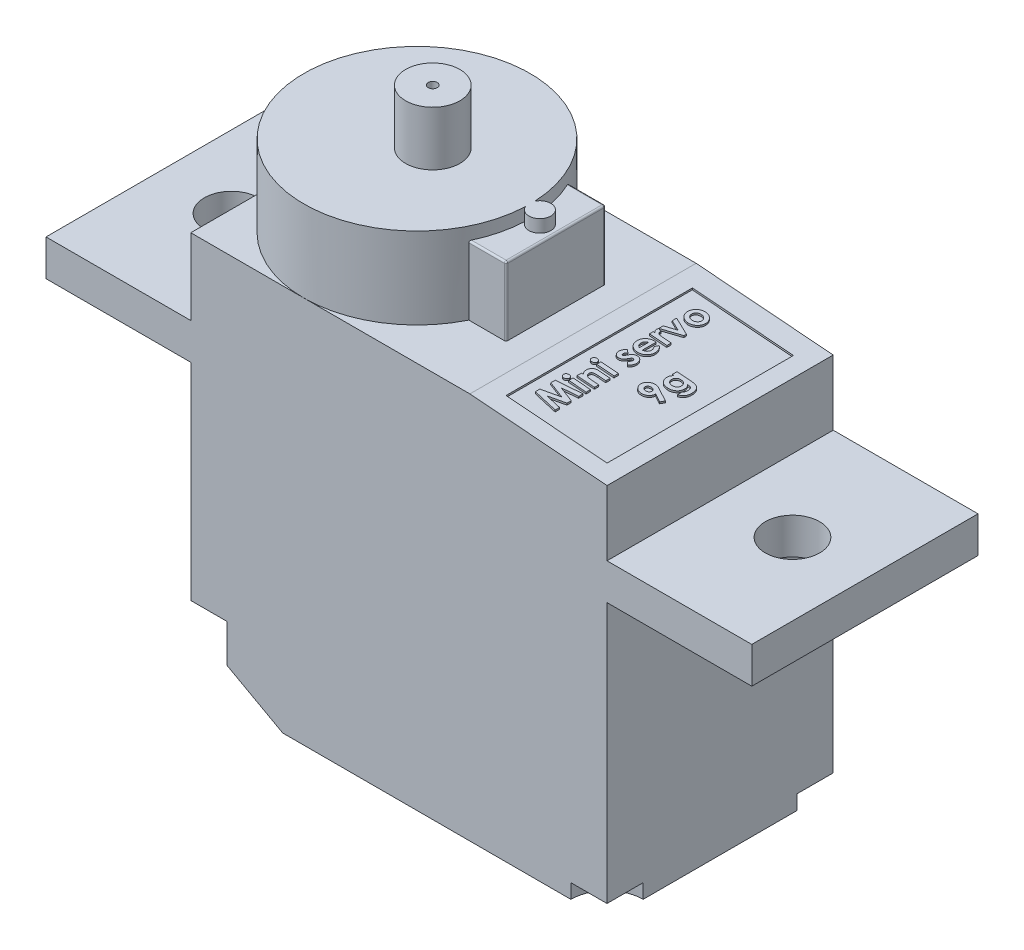
SolidWorks part; units mm, degrees
other "Camera1"
material "ABS"
ref_plane "Front Plane" through (0, 0, 0) normal (0, 0, 1) x (1, 0, 0)
ref_plane "Top Plane" through (0, 0, 0) normal (0, 1, 0) x (1, 0, 0)
ref_plane "Right Plane" through (0, 0, 0) normal (1, 0, 0) x (0, 0, -1)
sketch "Sketch1" plane through (0, 0, 0) normal (0, 1, 0) x (1, 0, 0)
  line L1 (11.5, -6.25) -> (-11.5, -6.25)
  line L2 (11.5, -6.25) -> (11.5, 6.25)
  line L3 (11.5, 6.25) -> (-11.5, 6.25)
  line L4 (-11.5, -6.25) -> (-11.5, 6.25)
  line L5 (11.5, -6.25) -> (-11.5, 6.25) construction
  line L6 (11.5, 6.25) -> (-11.5, -6.25) construction
  point P0 (0, 0)
  dimension "D1" = 12.5
  dimension "D2" = 23
extrude "Boss-Extrude1" add sketch "Sketch1" along normal blind 15.2
sketch "Sketch2" plane through (0, 15.2, 0) normal (0, 1, 0) x (1, 0, 0)
  line L0 (11.5, -6.25) -> (11.5, 6.25) construction
  line L1 (19.5, -6.25) -> (-19.5, -6.25)
  line L2 (19.5, -6.25) -> (19.5, 6.25)
  line L3 (19.5, 6.25) -> (-19.5, 6.25)
  line L4 (-19.5, -6.25) -> (-19.5, 6.25)
  line L5 (19.5, -6.25) -> (-19.5, 6.25) construction
  line L6 (19.5, 6.25) -> (-19.5, -6.25) construction
  point P0 (0, 0)
  dimension "D1" = 8
  dimension "D2" = 12.5
extrude "Boss-Extrude2" add sketch "Sketch2" along normal blind 2
sketch "Sketch3" plane through (0, 17.2, 0) normal (0, 1, 0) x (1, 0, 0)
  line L0 (19.5, 6.25) -> (-19.5, 6.25) construction
  line L1 (11.5, -6.25) -> (-11.5, -6.25)
  line L2 (11.5, -6.25) -> (11.5, 6.25)
  line L3 (11.5, 6.25) -> (-11.5, 6.25)
  line L4 (-11.5, -6.25) -> (-11.5, 6.25)
  line L5 (11.5, -6.25) -> (-11.5, 6.25) construction
  line L6 (11.5, 6.25) -> (-11.5, -6.25) construction
  point P0 (0, 0)
  dimension "D1" = 23
extrude "Boss-Extrude3" add sketch "Sketch3" along normal blind 4.2
sketch "Sketch4" plane through (0, 0, 6.25) normal (0, 0, 1) x (1, 0, 0)
  line L0 (11.5, 20.8) -> (3.9237, 21.4)
  line L1 (11.5, 21.4) -> (11.5, 17.2) construction
  line L2 (-11.5, 21.4) -> (11.5, 21.4) construction
  line L3 (3.9237, 21.4) -> (11.5, 21.4)
  line L4 (11.5, 21.4) -> (11.5, 20.8)
  dimension "D1" = 3.6
  dimension "D2" = 7.6
extrude "Cut-Extrude1" cut sketch "Sketch4" against normal through all
sketch "Sketch5" plane through (0, 21.4, 0) normal (0, 1, 0) x (1, 0, 0)
  line L0 (3.9237, 6.25) -> (-11.5, 6.25) construction
  line L2 (-11.5, 6.25) -> (-11.5, -6.25) construction
  line L3 (-11.5, -6.25) -> (3.9237, -6.25) construction
  circle A0 centre (-5.25, 0) radius 6.25
extrude "Boss-Extrude4" add sketch "Sketch5" along normal blind 4.5
sketch "Sketch6" plane through (0, 21.4, 0) normal (0, 1, 0) x (1, 0, 0)
  line L0 (3.9237, 6.25) -> (3.9237, -6.25) construction
  line L1 (-2.4237, -2.75) -> (2.4237, -2.75)
  line L2 (-2.4237, -2.75) -> (-2.4237, 2.75)
  line L3 (-2.4237, 2.75) -> (2.4237, 2.75)
  line L4 (2.4237, -2.75) -> (2.4237, 2.75)
  line L5 (-2.4237, -2.75) -> (2.4237, 2.75) construction
  line L6 (-2.4237, 2.75) -> (2.4237, -2.75) construction
  point P0 (0, 0)
  dimension "D1" = 1.5
  dimension "D2" = 5.5
extrude "Boss-Extrude5" add sketch "Sketch6" along normal blind 3.8
sketch "Sketch7" plane through (0, 25.2, 0) normal (0, 1, 0) x (1, 0, 0)
  circle A0 centre (1.5423, 0) radius 0.6059
extrude "Boss-Extrude7" add sketch "Sketch7" along normal up to surface (0.7 mm away) up to face at (-5.25, 25.9, 6.25)
sketch "Sketch8" plane through (0, 25.9, 0) normal (0, 1, 0) x (1, 0, 0)
  circle A0 centre (-4.3789, 0) radius 1.5
extrude "Boss-Extrude8" add sketch "Sketch8" along normal blind 3
sketch "Sketch9" plane through (0, 0, 6.25) normal (0, 0, 1) x (1, 0, 0)
  line L0 (-11.5, 0) -> (-6.4206, 0)
  line L1 (-11.5, 0) -> (11.5, 0) construction
  line L2 (-6.4206, 0) -> (-11.5, 2.8)
  line L3 (-11.5, 15.2) -> (-11.5, 0) construction
  line L4 (-11.5, 2.8) -> (-11.5, 0)
  dimension "D1" = 5.8
  dimension "D2" = 2.8
extrude "Cut-Extrude2" cut sketch "Sketch9" against normal through all
sketch "Sketch13" plane through (0, 28.9, 0) normal (0, 1, 0) x (1, 0, 0)
  circle A0 centre (-4.3789, 0) radius 0.25
  dimension "D1" = 0.5
extrude "Cut-Extrude3" cut sketch "Sketch13" against normal up to surface (7.5 mm away) up to face at (-9.8481, 21.4, 4.5981)
sketch "Sketch15" plane through (0, 0, 0) normal (0, -1, 0) x (1, 0, 0)
  line L0 (11.5, 6.25) -> (11.5, -6.25) construction
  line L1 (-6.4206, 6.25) -> (11.5, 6.25) construction
  line L2 (9.5, 6.25) -> (11.5, 6.25)
  line L3 (11.5, 6.25) -> (11.5, 4.25)
  line L4 (4.5258, 0) -> (-4.7559, 0) construction
  line L5 (11.5, -6.25) -> (11.5, -4.25)
  line L6 (9.5, -6.25) -> (11.5, -6.25)
  arc A0 (11.5, 4.25) -> (9.5, 6.25) centre (11.5, 6.25) cw
  arc A1 (11.5, -4.25) -> (9.5, -6.25) centre (11.5, -6.25) ccw
  dimension "D1" = 2
extrude "Cut-Extrude12" cut sketch "Sketch15" against normal blind 0.8
sketch "Sketch16" plane through (0, 0, 0) normal (0, -1, 0) x (1, 0, 0)
  line L0 (-6.4206, 6.25) -> (-11.5, 6.25) construction
  line L1 (-11.5, -6.25) -> (-11.5, 6.25) construction
  line L2 (-11.5, -6.25) -> (-11.5, 6.25) construction
  line L3 (-11.5, 4.25) -> (-11.5, 6.25)
  line L4 (-11.5, 6.25) -> (-9.5, 6.25)
  line L5 (-1.3995, 0) -> (2.6342, 0) construction
  line L6 (-11.5, -6.25) -> (-9.5, -6.25)
  line L7 (-11.5, -4.25) -> (-11.5, -6.25)
  arc A0 (-9.5, 6.25) -> (-11.5, 4.25) centre (-11.5, 6.25) cw
  arc A1 (-9.5, -6.25) -> (-11.5, -4.25) centre (-11.5, -6.25) ccw
  dimension "D1" = 2
extrude "Cut-Extrude13" cut sketch "Sketch16" against normal blind 3.8
sketch "Sketch17" plane through (1.7087, 21.5754, 0) normal (0.0789, 0.9969, 0) x (0.9969, -0.0789, 0)
  line L1 (8.822, -5.25) -> (3.222, -5.25)
  line L2 (8.822, -5.25) -> (8.822, 5.05)
  line L3 (8.822, 5.05) -> (3.222, 5.05)
  line L4 (3.222, -5.25) -> (3.222, 5.05)
  line L8 (2.222, 6.25) -> (2.222, -6.25) construction
  line L9 (9.822, 6.25) -> (9.822, -6.25) construction
  line L10 (2.222, -6.25) -> (9.822, -6.25) construction
  dimension "D1" = 1
  dimension "D2" = 1
  dimension "D3" = 1
  dimension "D4" = 10.3
extrude "Cut-Extrude14" cut sketch "Sketch17" against normal blind 0.1
sketch "Sketch19" plane through (1.7008, 21.4757, 0) normal (0.0789, 0.9969, 0) x (0.9969, -0.0789, 0)
  line L0 (5.1279, -5.25) -> (5.1279, 5.05) construction
  line L4 (3.222, -5.25) -> (8.822, -5.25) construction
  line L5 (8.822, 5.05) -> (3.222, 5.05) construction
  line L6 (7.5214, 5.05) -> (7.5214, -5.25) construction
  text T0 "<b>Mini servo</b>" font "Century Gothic" height in points 5
  text T1 "<b>9g</b>" font "Century Gothic" height in points 5
extrude "Boss-Extrude9" add sketch "Sketch19" along normal up to surface (0.1 mm away) up to face at (7.7119, 21.1, 0.1)
fillet "Fillet3" radius 0.1 5 edges at (2.4237, 25.2, 0) (1.3931, 25.2, 2.75) (2.4237, 23.3, 2.75) (2.4237, 23.3, -2.75) (1.3931, 25.2, -2.75)
hole_wizard "Ø3.0 (3) Diameter Hole1" positions "Sketch23" profile "Sketch20" hole size "Ø3.0" standard "ISO" end condition through all
sketch "Sketch23" plane through (0, 17.2, 0) normal (0, 1, 0) x (1, 0, 0)
  line L0 (-11.5, 6.25) -> (-11.5, 0) construction
  point P0 (-15.5, 0)
  dimension "D1" = 4
sketch "Sketch20" plane through (-15.5, 17.2, 0) normal (1, 0, 0) x (0, 0, 1)
  line L0 (0, 0) -> (0, 17.2)
  line L1 (0, 17.2) -> (1.5, 17.2)
  line L2 (1.5, 17.2) -> (1.5, 0)
  line L5 (1.5, 0) -> (0, 0)
  line L11 (0, -6.35) -> (0, 107.95) construction
  dimension "Thru Hole Dia." = 3
  dimension "Thru Hole Depth" = 17.2
mirror "Mirror1" about plane through (0, 0, 0) normal (1, 0, 0) of "Ø3.0 (3) Diameter Hole1"
